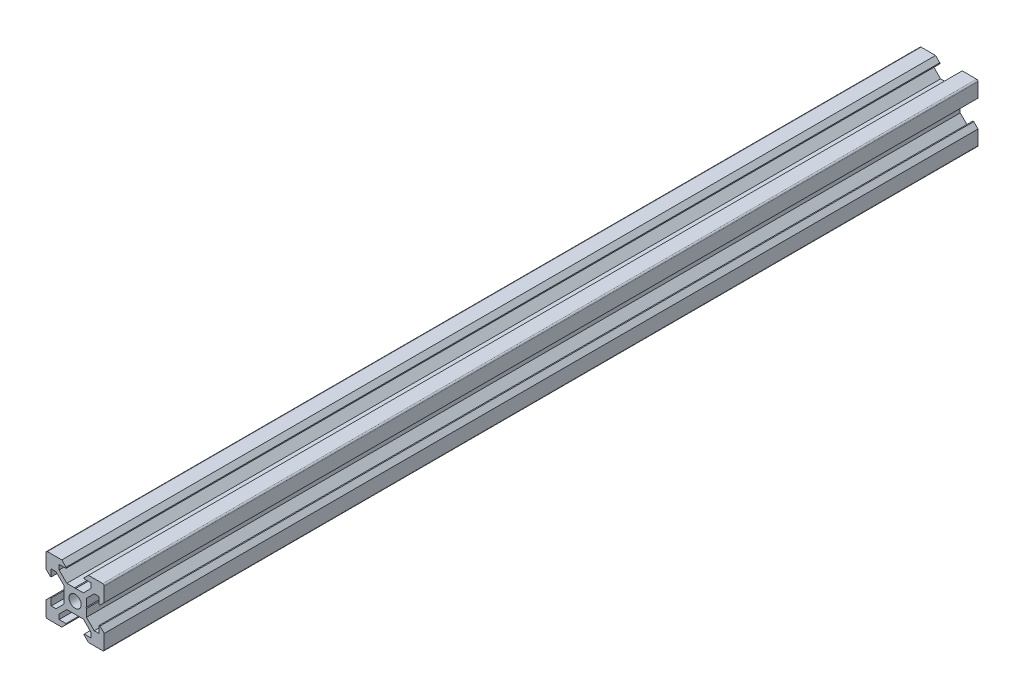
SolidWorks part; units mm, degrees
material "6061-T6 (SS)"
ref_plane "Front Plane" through (0, 0, 0) normal (0, 0, 1) x (1, 0, 0)
ref_plane "Top Plane" through (0, 0, 0) normal (0, 1, 0) x (1, 0, 0)
ref_plane "Right Plane" through (0, 0, 0) normal (1, 0, 0) x (0, 0, -1)
sketch "Sketch1" plane through (0, 0, 0) normal (0, 0, 1) x (1, 0, 0)
  line L1 (9.5, -10) -> (-9.5, -10)
  line L2 (10, -9.5) -> (10, 9.5)
  line L3 (9.5, 10) -> (-9.5, 10)
  line L4 (-10, -9.5) -> (-10, 9.5)
  line L5 (10, -10) -> (-10, 10) construction
  line L6 (10, 10) -> (-10, -10) construction
  circle A0 centre (0, 0) radius 2.1
  arc A1 (-9.5, 10) -> (-10, 9.5) centre (-9.5, 9.5) ccw
  arc A2 (10, 9.5) -> (9.5, 10) centre (9.5, 9.5) ccw
  arc A3 (9.5, -10) -> (10, -9.5) centre (9.5, -9.5) ccw
  arc A4 (-9.5, -10) -> (-10, -9.5) centre (-9.5, -9.5) cw
  point P0 (0, 0)
  line B0 (0, 0) -> (0, 10) construction
  line B1 (0, 3.69) -> (-0.21, 3.9)
  line B2 (-0.21, 3.9) -> (-2.8393, 3.9)
  line B3 (-2.8393, 3.9) -> (-5.5, 6.5607)
  line B4 (-5.5, 6.5607) -> (-5.5, 8.2)
  line B5 (-5.5, 8.2) -> (-3.125, 8.2)
  line B6 (-3.125, 8.2) -> (-3.125, 8.545)
  line B7 (-3.125, 8.545) -> (-4.58, 10)
  line B8 (-4.58, 10) -> (4.58, 10)
  line B9 (0, 0) -> (-5.9132, 5.9132) construction
  line B10 (3.125, 8.545) -> (4.58, 10)
  line B11 (3.125, 8.2) -> (3.125, 8.545)
  line B12 (5.5, 8.2) -> (3.125, 8.2)
  line B13 (5.5, 6.5607) -> (5.5, 8.2)
  line B14 (2.8393, 3.9) -> (5.5, 6.5607)
  line B15 (0.21, 3.9) -> (2.8393, 3.9)
  line B16 (0, 3.69) -> (0.21, 3.9)
  line B17 (0, 0) -> (-10, 0) construction
  line B18 (-3.69, 0) -> (-3.9, -0.21)
  line B19 (-3.9, -0.21) -> (-3.9, -2.8393)
  line B20 (-3.9, -2.8393) -> (-6.5607, -5.5)
  line B21 (-6.5607, -5.5) -> (-8.2, -5.5)
  line B22 (-8.2, -5.5) -> (-8.2, -3.125)
  line B23 (-8.2, -3.125) -> (-8.545, -3.125)
  line B24 (-8.545, -3.125) -> (-10, -4.58)
  line B25 (-10, -4.58) -> (-10, 4.58)
  line B26 (0, 0) -> (-5.9132, -5.9132) construction
  line B27 (-8.545, 3.125) -> (-10, 4.58)
  line B28 (-8.2, 3.125) -> (-8.545, 3.125)
  line B29 (-8.2, 5.5) -> (-8.2, 3.125)
  line B30 (-6.5607, 5.5) -> (-8.2, 5.5)
  line B31 (-3.9, 2.8393) -> (-6.5607, 5.5)
  line B32 (-3.9, 0.21) -> (-3.9, 2.8393)
  line B33 (-3.69, 0) -> (-3.9, 0.21)
  line B34 (0, 0) -> (0, -10) construction
  line B35 (0, -3.69) -> (0.21, -3.9)
  line B36 (0.21, -3.9) -> (2.8393, -3.9)
  line B37 (2.8393, -3.9) -> (5.5, -6.5607)
  line B38 (5.5, -6.5607) -> (5.5, -8.2)
  line B39 (5.5, -8.2) -> (3.125, -8.2)
  line B40 (3.125, -8.2) -> (3.125, -8.545)
  line B41 (3.125, -8.545) -> (4.58, -10)
  line B42 (4.58, -10) -> (-4.58, -10)
  line B43 (0, 0) -> (5.9132, -5.9132) construction
  line B44 (-3.125, -8.545) -> (-4.58, -10)
  line B45 (-3.125, -8.2) -> (-3.125, -8.545)
  line B46 (-5.5, -8.2) -> (-3.125, -8.2)
  line B47 (-5.5, -6.5607) -> (-5.5, -8.2)
  line B48 (-2.8393, -3.9) -> (-5.5, -6.5607)
  line B49 (-0.21, -3.9) -> (-2.8393, -3.9)
  line B50 (0, -3.69) -> (-0.21, -3.9)
  line B51 (0, 0) -> (10, 0) construction
  line B52 (3.69, 0) -> (3.9, 0.21)
  line B53 (3.9, 0.21) -> (3.9, 2.8393)
  line B54 (3.9, 2.8393) -> (6.5607, 5.5)
  line B55 (6.5607, 5.5) -> (8.2, 5.5)
  line B56 (8.2, 5.5) -> (8.2, 3.125)
  line B57 (8.2, 3.125) -> (8.545, 3.125)
  line B58 (8.545, 3.125) -> (10, 4.58)
  line B59 (10, 4.58) -> (10, -4.58)
  line B60 (0, 0) -> (5.9132, 5.9132) construction
  line B61 (8.545, -3.125) -> (10, -4.58)
  line B62 (8.2, -3.125) -> (8.545, -3.125)
  line B63 (8.2, -5.5) -> (8.2, -3.125)
  line B64 (6.5607, -5.5) -> (8.2, -5.5)
  line B65 (3.9, -2.8393) -> (6.5607, -5.5)
  line B66 (3.9, -0.21) -> (3.9, -2.8393)
  line B67 (3.69, 0) -> (3.9, -0.21)
  dimension "D1" = 4.2
  dimension "D3" = 0.5
  dimension "D2" = 20
sketch_block_instance "V Slot 1-4"
sketch_block "V Slot 1" parameters "D1"=10, "D2"=11, "D3"=4.3, "D4"=1.8, "D5"=0.21, "D6"=45, "D7"=9.16, "D8"=1.5, "D9"=6.25
sketch_block_instance "V Slot 1-5"
sketch_block_instance "V Slot 1-6"
sketch_block_instance "V Slot 1-7"
extrude "Boss-Extrude1" add sketch "Sketch1" along normal blind 300 contours B67 B52 B53 B54 B55 B56 B57 B58 L2 A2 L3 B10 B11 B12 B13 B14 B15 B16 B1 B2 B3 B4 B5 B6 B7 A1 L4 B27 B28 B29 B30 B31 B32 B33 B18 B19 B20 B21 B22 B23 B24 A4 L1 B44 B45 B46 B47 B48 B49
